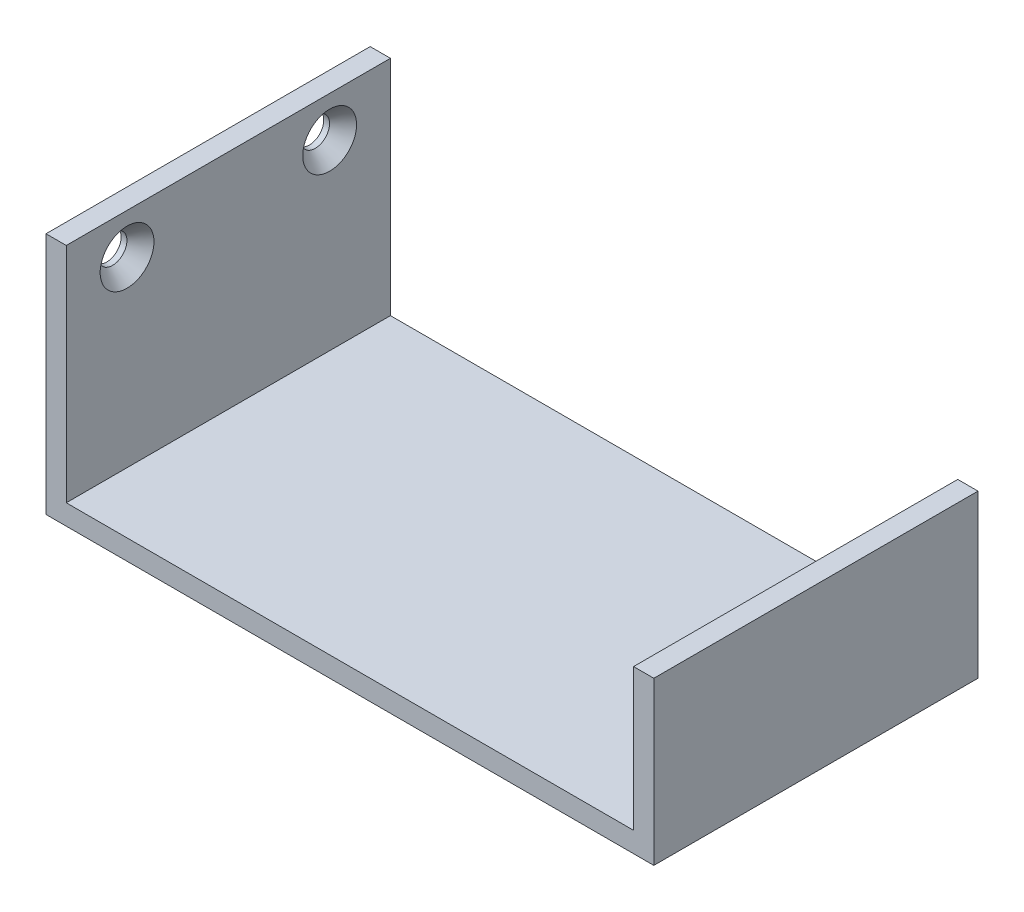
SolidWorks part; units mm, degrees
ref_plane "Front Plane" through (0, 0, 0) normal (0, 0, 1) x (1, 0, 0)
ref_plane "Top Plane" through (0, 0, 0) normal (0, 1, 0) x (1, 0, 0)
ref_plane "Right Plane" through (0, 0, 0) normal (1, 0, 0) x (0, 0, -1)
sketch "Sketch1" plane through (0, 0, 0) normal (0, 0, 1) x (1, 0, 0)
  line L0 (0, 0) -> (0, 38.1)
  line L1 (0, 38.1) -> (3.175, 38.1)
  line L2 (3.175, 38.1) -> (3.175, 3.175)
  line L3 (3.175, 3.175) -> (92.075, 3.175)
  line L4 (92.075, 3.175) -> (92.075, 25.4)
  line L5 (92.075, 25.4) -> (95.25, 25.4)
  line L6 (95.25, 25.4) -> (95.25, 0)
  line L7 (95.25, 0) -> (0, 0)
  dimension "D1" = 3.175
  dimension "D2" = 3.175
  dimension "D3" = 88.9
  dimension "D4" = 38.1
  dimension "D5" = 25.4
extrude "Boss-Extrude1" add sketch "Sketch1" along normal blind 50.8
hole_wizard "CSK for #8 Flat Head Machine Screw1" positions "Sketch2" profile "Sketch3" countersink size "#8" standard "ANSI Inch" end condition through all
sketch "Sketch2" plane through (3.175, 0, 0) normal (1, 0, 0) x (0, 0, -1)
  line L0 (-50.8, 31.75) -> (0, 31.75) construction
  line L1 (-50.8, 3.175) -> (-50.8, 38.1) construction
  line L2 (0, 3.175) -> (0, 38.1) construction
  line L4 (-50.8, 38.1) -> (0, 38.1) construction
  point P0 (-41.275, 31.75)
  point P2 (-9.525, 31.75)
  point P14 (0, 0)
  point P15 (0, 0)
  dimension "D1" = 9.525
  dimension "D2" = 9.525
  dimension "D3" = 6.35
sketch "Sketch3" plane through (3.175, 31.75, 41.275) normal (0, 1, 0) x (0, 0, -1)
  line L0 (0, 0) -> (0, 3.175)
  line L1 (0, 3.175) -> (2.2479, 3.175)
  line L2 (2.2479, 3.175) -> (2.2479, 2.2645)
  line L3 (2.2479, 2.2645) -> (4.2164, 0)
  line L5 (4.2164, 0) -> (0, 0)
  line L6 (-2.2479, 2.2645) -> (-4.2164, 0) construction
  line L11 (0, -6.35) -> (0, 107.95) construction
  dimension "Thru Hole Dia." = 4.4958
  dimension "Thru Hole Depth" = 3.175
  dimension "Near C'Sink Dia." = 8.4328
  dimension "Near C'Sink Angle" = 82
